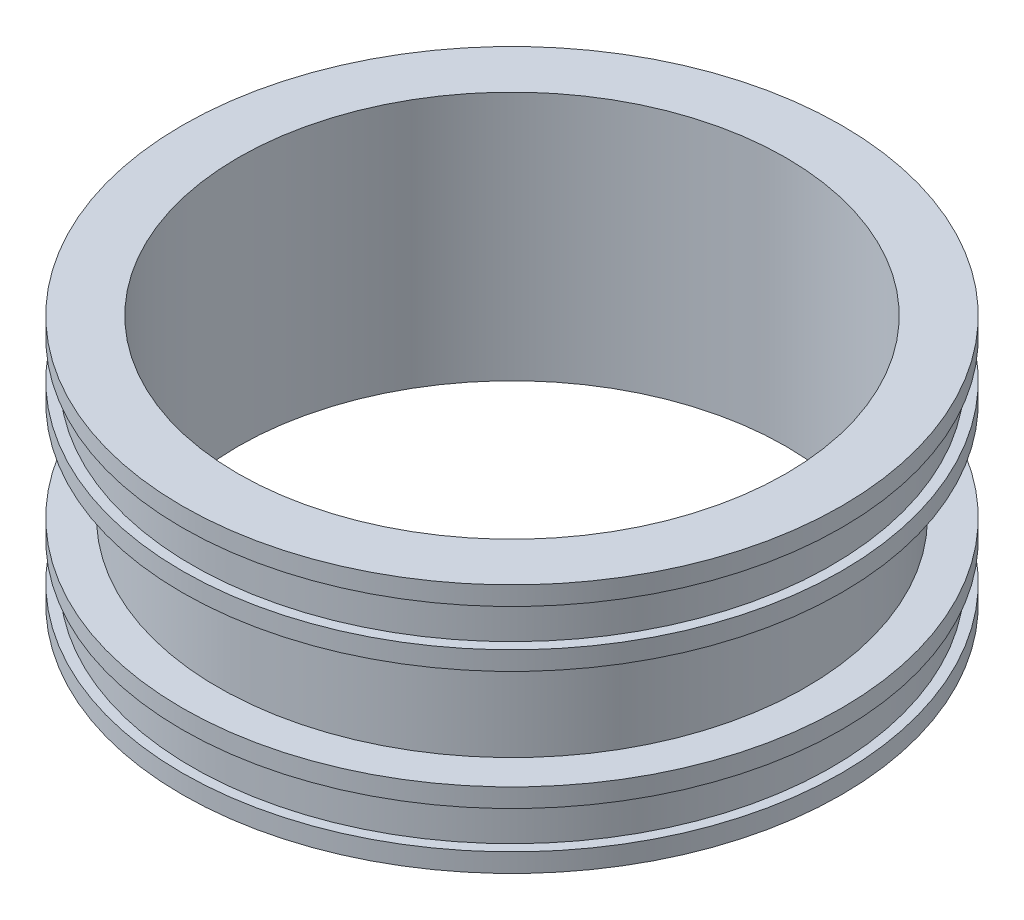
SolidWorks part; units mm, degrees
material "AISI 1020"
ref_plane "Plano frontal" through (0, 0, 0) normal (0, 0, 1) x (1, 0, 0)
ref_plane "Plano superior" through (0, 0, 0) normal (0, 1, 0) x (1, 0, 0)
ref_plane "Plano direito" through (0, 0, 0) normal (1, 0, 0) x (0, 0, -1)
sketch "Esboço1" plane through (0, 0, 0) normal (0, 0, 1) x (1, 0, 0)
  line L0 (0, 0) -> (0, 327.1613) construction
  line L1 (0, 0) -> (502.3995, 0) construction
  line L2 (109.54, 100) -> (131.9, 100)
  line L3 (131.9, 100) -> (131.9, 92.5)
  line L4 (131.9, 70) -> (117.54, 70)
  line L5 (117.54, 70) -> (117.54, 30)
  line L6 (117.54, 30) -> (131.9, 30)
  line L7 (131.9, 30) -> (131.9, 22.5)
  line L8 (131.9, 0) -> (109.54, 0)
  line L9 (109.54, 0) -> (109.54, 100)
  line L10 (131.9, 92.5) -> (127.9, 92.5)
  line L11 (127.9, 92.5) -> (127.9, 77.5)
  line L12 (127.9, 77.5) -> (131.9, 77.5)
  line L13 (109.54, 50) -> (131.9, 50) construction
  line L14 (131.9, 77.5) -> (131.9, 70)
  line L15 (127.9, 22.5) -> (131.9, 22.5)
  line L16 (127.9, 7.5) -> (127.9, 22.5)
  line L17 (131.9, 7.5) -> (127.9, 7.5)
  line L18 (131.9, 7.5) -> (131.9, 0)
  point P22 (117.54, 50)
  dimension "D1" = 219.08
  dimension "D2" = 4
  dimension "D3" = 15
  dimension "D4" = 30
  dimension "250" = 263.8
  dimension "D6" = 8
  dimension "D7" = 100
revolve "Revolução1" add sketch "Esboço1" angle 360 about L0
